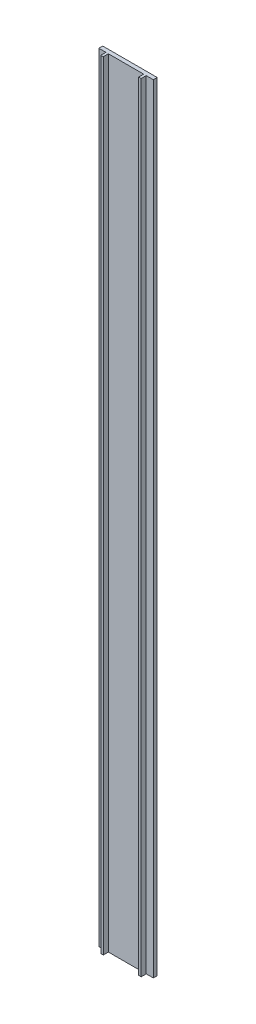
SolidWorks part; units mm, degrees
ref_plane "Front" through (0, 0, 0) normal (0, 0, 1) x (1, 0, 0)
ref_plane "Top" through (0, 0, 0) normal (0, 1, 0) x (1, 0, 0)
ref_plane "Right" through (0, 0, 0) normal (1, 0, 0) x (0, 0, -1)
sketch "Sketch1" plane through (0, 0, 0) normal (0, 0, 1) x (1, 0, 0)
  line L1 (-35, -500) -> (35, -500)
  line L2 (-35, -500) -> (-35, 500)
  line L3 (-35, 500) -> (35, 500)
  line L4 (35, -500) -> (35, 500)
  line L5 (-35, -500) -> (35, 500) construction
  line L6 (-35, 500) -> (35, -500) construction
  point P0 (0, 0)
  dimension "D1" = 1000
  dimension "D2" = 70
extrude "Boss-Extrude1" add sketch "Sketch1" along normal blind 5
sketch "Sketch3" plane through (0, 0, 5) normal (0, 0, 1) x (1, 0, 0)
  line L0 (35, 500) -> (-35, 500) construction
  line L1 (-22.695, -500) -> (-25.905, -500)
  line L2 (-22.695, -500) -> (-22.695, 500)
  line L3 (-22.695, 500) -> (-25.905, 500)
  line L4 (-25.905, -500) -> (-25.905, 500)
  line L5 (-35, -500) -> (35, -500) construction
  line L6 (25.905, 500) -> (22.695, 500)
  line L7 (25.905, 500) -> (25.905, -500)
  line L8 (25.905, -500) -> (22.695, -500)
  line L9 (22.695, 500) -> (22.695, -500)
  line L10 (0, -500) -> (0, 500) construction
  point P14 (0, 0)
  point P15 (0, 0)
  point P16 (0, 0)
  point P17 (0, 0)
  dimension "D1" = 3.21
  dimension "D2" = 3.21
  dimension "D3" = 22.695
  dimension "D4" = 22.695
extrude "Boss-Extrude2" add sketch "Sketch3" along normal blind 6.5
